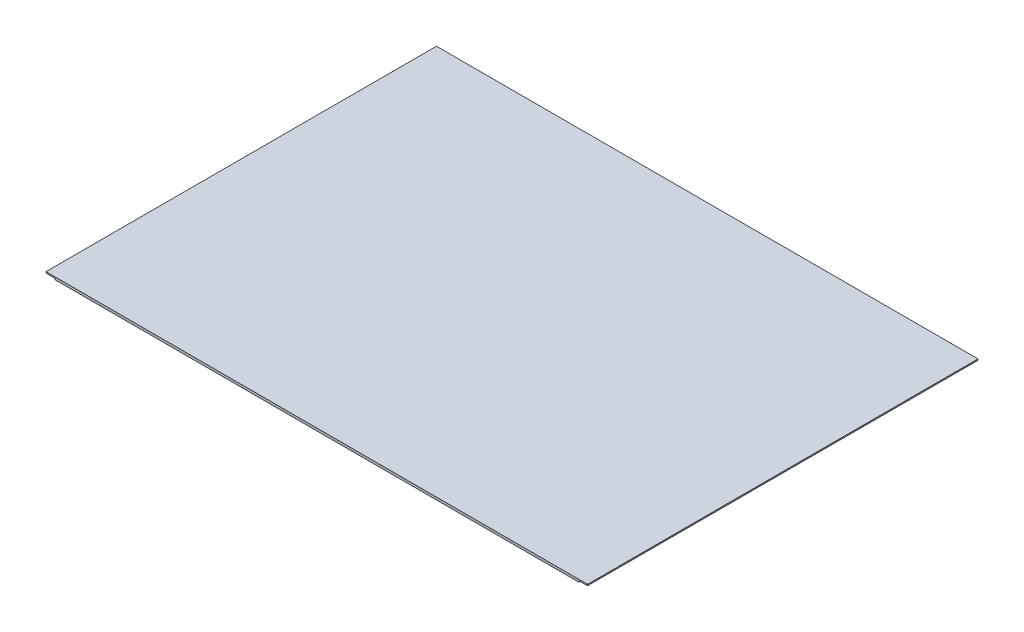
SolidWorks part; units mm, degrees
material "7050-T73510"
ref_plane "Front Plane" through (0, 0, 0) normal (0, 0, 1) x (1, 0, 0)
ref_plane "Top Plane" through (0, 0, 0) normal (0, 1, 0) x (1, 0, 0)
ref_plane "Right Plane" through (0, 0, 0) normal (1, 0, 0) x (0, 0, -1)
sketch "Sketch1" plane through (0, 0, 0) normal (0, 1, 0) x (1, 0, 0)
  line L1 (-215, 155) -> (215, 155)
  line L2 (-215, 155) -> (-215, -155)
  line L3 (-215, -155) -> (215, -155)
  line L4 (215, 155) -> (215, -155)
  line L5 (-215, 155) -> (215, -155) construction
  line L6 (-215, -155) -> (215, 155) construction
  point P0 (0, 0)
  dimension "D1" = 430
  dimension "D2" = 310
extrude "Boss-Extrude1" add sketch "Sketch1" along normal blind 2
sketch "Sketch2" plane through (0, 0, 155) normal (0, 0, 1) x (1, 0, 0)
  line L0 (-215, 1) -> (-208, 1)
  line L1 (-215, 2) -> (-215, 0) construction
  line L2 (-208, 1) -> (-208, 0)
  line L3 (-215, 0) -> (215, 0) construction
  line L4 (-208, 0) -> (-215, 0)
  line L5 (-215, 0) -> (-215, 1)
  line L6 (0, 2) -> (0, 0) construction
  line L7 (-215, 2) -> (215, 2) construction
  line L8 (215, 0) -> (215, 1)
  line L9 (208, 0) -> (215, 0)
  line L10 (208, 1) -> (208, 0)
  line L11 (215, 1) -> (208, 1)
  dimension "D1" = 7
extrude "Cut-Extrude1" cut sketch "Sketch2" against normal through all
